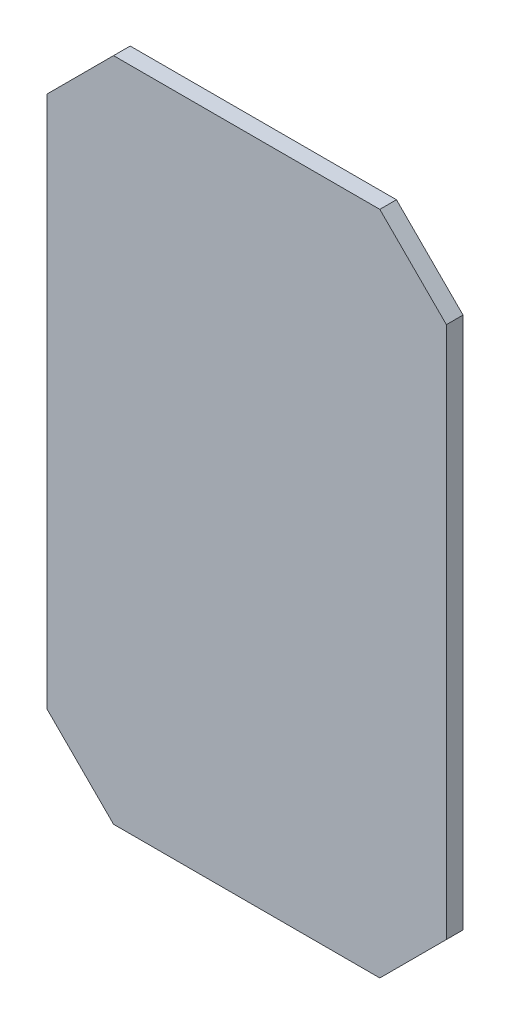
SolidWorks part; units mm, degrees
material "Thornel Mat VMA"
ref_plane "Front Plane" through (0, 0, 0) normal (0, 0, 1) x (1, 0, 0)
ref_plane "Top Plane" through (0, 0, 0) normal (0, 1, 0) x (1, 0, 0)
ref_plane "Right Plane" through (0, 0, 0) normal (1, 0, 0) x (0, 0, -1)
sketch "Sketch1" plane through (0, 0, 0) normal (0, 0, 1) x (1, 0, 0)
  line L0 (-11.2921, 0) -> (1.4079, 12.7)
  line L1 (1.4079, 12.7) -> (52.2079, 12.7)
  line L2 (-11.2921, 0) -> (-11.2921, -101.6)
  line L3 (1.4079, -114.3) -> (52.2079, -114.3)
  line L4 (64.9079, 0) -> (64.9079, -101.6)
  line L5 (52.2079, 12.7) -> (64.9079, 0)
  line L6 (-11.2921, -101.6) -> (1.4079, -114.3)
  line L7 (52.2079, -114.3) -> (64.9079, -101.6)
  circle A0 centre (1.4079, 0) radius 1.5875 construction
  circle A1 centre (52.2079, 0) radius 2.8575 construction
  circle A2 centre (52.2079, -101.6) radius 2.8575 construction
  point P0 (-11.2921, 12.7)
  point P1 (64.9079, -114.3)
  point P2 (-11.2921, -114.3)
  point P3 (64.9079, 12.7)
  dimension "D1" = 12.7
  dimension "D4" = 12.7
  dimension "D2" = 12.7
  dimension "D3" = 12.7
extrude "Boss-Extrude1" add sketch "Sketch1" along normal blind 3.175 contours L1 L5 L4 L7 L3 L6 L2 L0
